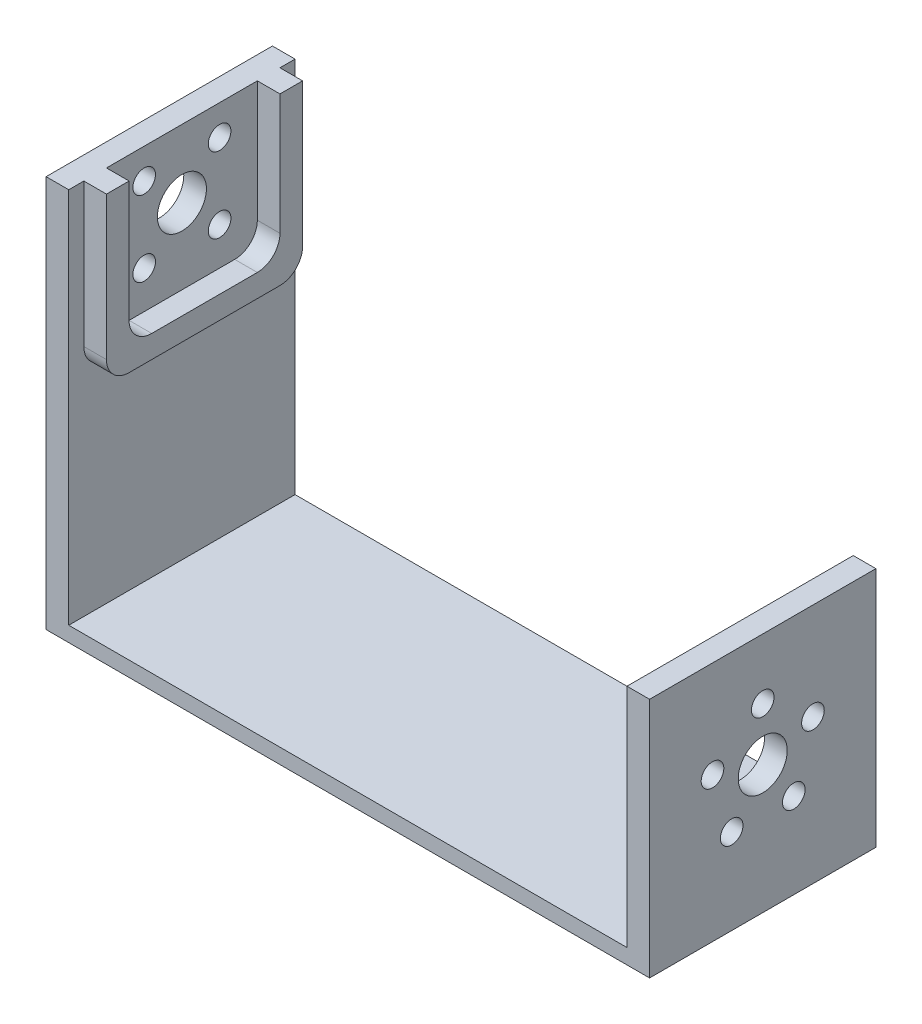
SolidWorks part; units mm, degrees
ref_plane "Front Plane" through (0, 0, 0) normal (0, 0, 1) x (1, 0, 0)
ref_plane "Top Plane" through (0, 0, 0) normal (0, 1, 0) x (1, 0, 0)
ref_plane "Right Plane" through (0, 0, 0) normal (1, 0, 0) x (0, 0, -1)
sketch "Sketch1" plane through (0, 0, 0) normal (0, 1, 0) x (1, 0, 0)
  line L1 (40, -15) -> (-40, -15)
  line L2 (40, -15) -> (40, 15)
  line L3 (40, 15) -> (-40, 15)
  line L4 (-40, -15) -> (-40, 15)
  line L5 (40, -15) -> (-40, 15) construction
  line L6 (40, 15) -> (-40, -15) construction
  point P0 (0, 0)
  dimension "D1" = 80
  dimension "D2" = 30
extrude "Chassis" add sketch "Sketch1" along normal blind 2
sketch "Sketch2" plane through (0, 2, 0) normal (0, 1, 0) x (1, 0, 0)
  line L0 (-40, -15) -> (40, -15) construction
  line L1 (-40, 15) -> (-37, 15)
  line L2 (-40, 15) -> (-40, -15)
  line L3 (-40, -15) -> (-37, -15)
  line L4 (-37, 15) -> (-37, -15)
  dimension "D1" = 3
extrude "TallValveWall" add sketch "Sketch2" along normal blind 50
sketch "Sketch3" plane through (0, 2, 0) normal (0, 1, 0) x (1, 0, 0)
  line L0 (40, 15) -> (-37, 15) construction
  line L1 (37, 15) -> (40, 15)
  line L2 (37, 15) -> (37, -15)
  line L3 (37, -15) -> (40, -15)
  line L4 (40, 15) -> (40, -15)
  dimension "D1" = 3
extrude "ShortValveWall" add sketch "Sketch3" along normal blind 30
sketch "Sketch4" plane through (-37, 0, 0) normal (1, 0, 0) x (0, 0, -1)
  line L0 (-15, 52) -> (15, 52) construction
  line L1 (-5, 48) -> (5, 48) construction
  line L2 (-5, 48) -> (-5, 38) construction
  line L3 (-5, 38) -> (5, 38) construction
  line L4 (5, 48) -> (5, 38) construction
  line L5 (-5, 48) -> (5, 38) construction
  line L6 (-5, 38) -> (5, 48) construction
  line L7 (-15, 2) -> (15, 2) construction
  line L8 (15, 52) -> (-15, 52) construction
  circle A0 centre (-5, 48) radius 1.5
  circle A1 centre (5, 48) radius 1.5
  circle A2 centre (5, 38) radius 1.5
  circle A3 centre (-5, 38) radius 1.5
  circle A4 centre (0, 43) radius 3.25
  point P0 (0, 43)
  point P8 (0, 52)
  dimension "D3" = 3
  dimension "D4" = 6.5
  dimension "D1" = 4
  dimension "D2" = 10
  dimension "D5" = 41
  dimension "D6" = 4
  dimension "D7" = 7.0711
  dimension "D8" = 7.0711
extrude "TallValveCut" cut sketch "Sketch4" against normal through all
sketch "Sketch6" plane through (40, 0, 0) normal (1, 0, 0) x (0, 0, -1)
  line L0 (-15, 32) -> (15, 32) construction
  line L1 (15, 2) -> (-15, 2) construction
  circle A0 centre (0, 17) radius 3.25
  circle A1 centre (0, 43) radius 3.25 construction
  circle A2 centre (0, 24) radius 1.5
  circle A3 centre (6.6574, 19.1631) radius 1.5
  circle A4 centre (4.1145, 11.3369) radius 1.5
  circle A5 centre (-4.1145, 11.3369) radius 1.5
  circle A6 centre (-6.6574, 19.1631) radius 1.5
  point P19 (0, 17)
  dimension "D1" = 15
  dimension "D2" = 7
  dimension "D3" = 3
  dimension "D5" = 6.5
  dimension "D6" = 15
  dimension "D4" = 5
extrude "ShortValveCut" cut sketch "Sketch6" against normal up to next
sketch "Sketch7" plane through (-37, 0, 0) normal (1, 0, 0) x (0, 0, -1)
  line L0 (-15, 52) -> (15, 52) construction
  line L1 (-13, 52) -> (-10, 52)
  line L2 (-13, 52) -> (-13, 30)
  line L4 (-10, 52) -> (-10, 33)
  line L5 (-10, 33) -> (10, 33)
  line L7 (-13, 30) -> (13, 30)
  line L10 (13, 30) -> (13, 52)
  line L11 (13, 52) -> (10, 52)
  line L12 (10, 33) -> (10, 52)
  circle A0 centre (0, 43) radius 3.25 construction
  point P4 (0, 33)
  point P16 (0, 52)
  dimension "D1" = 3
  dimension "D2" = 3
  dimension "D3" = 10
  dimension "D4" = 10
  dimension "D5" = 19
  dimension "D6" = 20
  dimension "D7" = 5
  dimension "D8" = 5
  dimension "D9" = 5
  dimension "D10" = 10
extrude "TallValveLip" add sketch "Sketch7" along normal blind 3
fillet "LipRounding" radius 3 4 edges at (-35.5, 33, -10) (-35.5, 33, 10) (-35.5, 30, -13) (-35.5, 30, 13)
